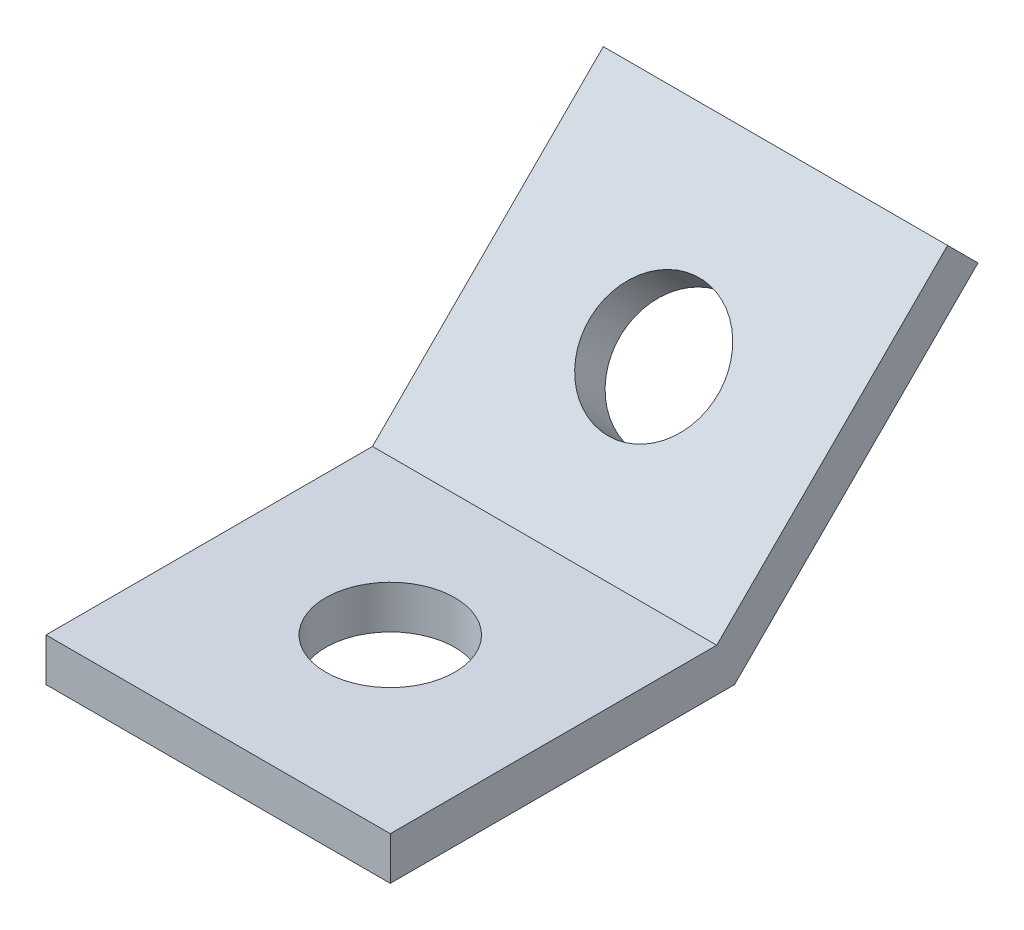
SolidWorks part; units mm, degrees
ref_plane "Front Plane" through (0, 0, 0) normal (0, 0, 1) x (1, 0, 0)
ref_plane "Top Plane" through (0, 0, 0) normal (0, 1, 0) x (1, 0, 0)
ref_plane "Right Plane" through (0, 0, 0) normal (1, 0, 0) x (0, 0, -1)
sketch "Sketch1" plane through (0, 0, 0) normal (1, 0, 0) x (0, 0, -1)
  line L0 (0, 0) -> (-25.4, 0)
  line L1 (-25.4, 0) -> (-25.4, 3.175)
  line L2 (-25.4, 3.175) -> (-1.3151, 3.175)
  line L3 (-1.3151, 3.175) -> (15.7154, 20.2056)
  line L4 (15.7154, 20.2056) -> (17.9605, 17.9605)
  line L5 (17.9605, 17.9605) -> (0, 0)
  dimension "D1" = 25.4
  dimension "D2" = 3.175
  dimension "D3" = 135
extrude "Boss-Extrude1" add sketch "Sketch1" along normal blind 25.4
sketch "Sketch2" plane through (0, 3.175, 0) normal (0, 1, 0) x (1, 0, 0)
  line L0 (12.7, -25.4) -> (12.7, -12.7) construction
  line L1 (25.4, -25.4) -> (0, -25.4) construction
  circle A0 centre (12.7, -12.7) radius 4.7625
  dimension "D1" = 9.525
  dimension "D2" = 12.7
extrude "Cut-Extrude1" cut sketch "Sketch2" against normal blind 25.4
sketch "Sketch3" plane through (0, 2.2451, 2.2451) normal (0, 0.7071, 0.7071) x (1, 0, 0)
  line L0 (12.7, 25.4) -> (12.7, 12.7) construction
  line L1 (25.4, 25.4) -> (0, 25.4) construction
  circle A0 centre (12.7, 12.7) radius 4.7625
  dimension "D1" = 9.525
  dimension "D2" = 12.7
extrude "Cut-Extrude2" cut sketch "Sketch3" against normal through all
